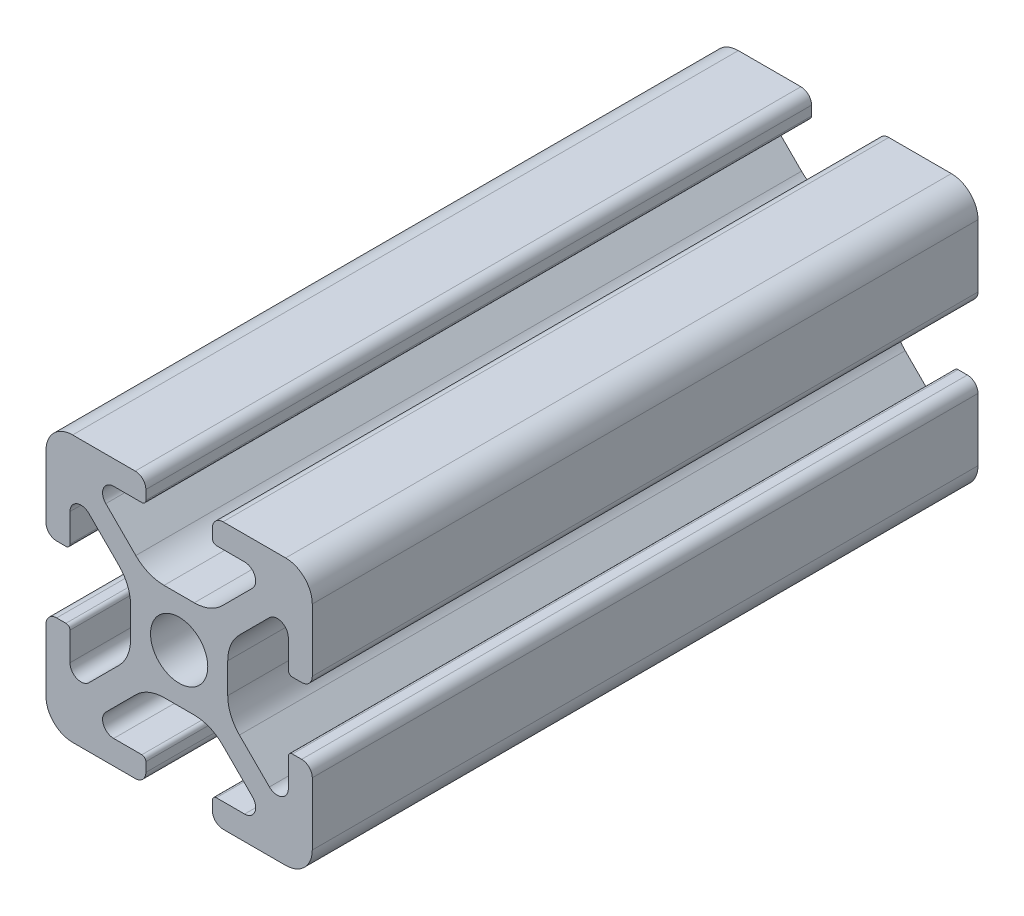
SolidWorks part; units mm, degrees
ref_plane "Front Plane" through (0, 0, 0) normal (0, 0, 1) x (1, 0, 0)
ref_plane "Top Plane" through (0, 0, 0) normal (0, 1, 0) x (1, 0, 0)
ref_plane "Right Plane" through (0, 0, 0) normal (1, 0, 0) x (0, 0, -1)
ref_plane "Plane1" through (0, 0, 0) normal (0, 0, -1) x (-1, 0, 0)
sketch "Sketch1" plane through (0, 0, 0) normal (0, 0, -1) x (-1, 0, 0)
  line L0 (-12.5, 0.8) -> (-12.5, 1.5)
  line L1 (-12.8, 1.8) -> (-14.9176, 1.8)
  line L2 (-15.5062, 3.221) -> (-13.2559, 5.4713)
  line L3 (-11.1346, 6.35) -> (-8.8654, 6.35)
  line L4 (-6.7441, 5.4713) -> (-4.4938, 3.221)
  line L5 (-5.0824, 1.8) -> (-7.2, 1.8)
  line L6 (-7.5, 1.5) -> (-7.5, 0.8)
  line L7 (-6.7, 0) -> (-2, 0)
  line L8 (0, 2) -> (0, 6.7)
  line L9 (-0.8, 7.5) -> (-1.5, 7.5)
  line L10 (-1.8, 7.2) -> (-1.8, 5.0824)
  line L11 (-3.221, 4.4938) -> (-5.4713, 6.7441)
  line L12 (-6.35, 8.8654) -> (-6.35, 11.1346)
  line L13 (-5.4713, 13.2559) -> (-3.221, 15.5062)
  line L14 (-1.8, 14.9176) -> (-1.8, 12.8)
  line L15 (-1.5, 12.5) -> (-0.8, 12.5)
  line L16 (0, 13.3) -> (0, 18)
  line L17 (-2, 20) -> (-6.7, 20)
  line L18 (-7.5, 19.2) -> (-7.5, 18.5)
  line L19 (-7.2, 18.2) -> (-5.0824, 18.2)
  line L20 (-4.4938, 16.779) -> (-6.7441, 14.5287)
  line L21 (-8.8654, 13.65) -> (-11.1346, 13.65)
  line L22 (-13.2559, 14.5287) -> (-15.5062, 16.779)
  line L23 (-14.9176, 18.2) -> (-12.8, 18.2)
  line L24 (-12.5, 18.5) -> (-12.5, 19.2)
  line L25 (-13.3, 20) -> (-18, 20)
  line L26 (-20, 18) -> (-20, 13.3)
  line L27 (-19.2, 12.5) -> (-18.5, 12.5)
  line L28 (-18.2, 12.8) -> (-18.2, 14.9176)
  line L29 (-16.779, 15.5062) -> (-14.5287, 13.2559)
  line L30 (-13.65, 11.1346) -> (-13.65, 8.8654)
  line L31 (-14.5287, 6.7441) -> (-16.779, 4.4938)
  line L32 (-18.2, 5.0824) -> (-18.2, 7.2)
  line L33 (-18.5, 7.5) -> (-19.2, 7.5)
  line L34 (-20, 6.7) -> (-20, 2)
  line L35 (-18, 0) -> (-13.3, 0)
  arc A0 (-12.5, 1.5) -> (-12.8, 1.8) centre (-12.8, 1.5) ccw
  arc A1 (-14.9176, 1.8) -> (-15.5062, 3.221) centre (-14.9176, 2.6324) cw
  arc A2 (-13.2559, 5.4713) -> (-11.1346, 6.35) centre (-11.1346, 3.35) cw
  arc A3 (-8.8654, 6.35) -> (-6.7441, 5.4713) centre (-8.8654, 3.35) cw
  arc A4 (-4.4938, 3.221) -> (-5.0824, 1.8) centre (-5.0824, 2.6324) cw
  arc A5 (-7.2, 1.8) -> (-7.5, 1.5) centre (-7.2, 1.5) ccw
  arc A6 (-7.5, 0.8) -> (-6.7, 0) centre (-6.7, 0.8) ccw
  arc A7 (-2, 0) -> (0, 2) centre (-2, 2) ccw
  arc A8 (0, 6.7) -> (-0.8, 7.5) centre (-0.8, 6.7) ccw
  arc A9 (-1.5, 7.5) -> (-1.8, 7.2) centre (-1.5, 7.2) ccw
  arc A10 (-1.8, 5.0824) -> (-3.221, 4.4938) centre (-2.6324, 5.0824) cw
  arc A11 (-5.4713, 6.7441) -> (-6.35, 8.8654) centre (-3.35, 8.8654) cw
  arc A12 (-6.35, 11.1346) -> (-5.4713, 13.2559) centre (-3.35, 11.1346) cw
  arc A13 (-3.221, 15.5062) -> (-1.8, 14.9176) centre (-2.6324, 14.9176) cw
  arc A14 (-1.8, 12.8) -> (-1.5, 12.5) centre (-1.5, 12.8) ccw
  arc A15 (-0.8, 12.5) -> (0, 13.3) centre (-0.8, 13.3) ccw
  arc A16 (0, 18) -> (-2, 20) centre (-2, 18) ccw
  arc A17 (-6.7, 20) -> (-7.5, 19.2) centre (-6.7, 19.2) ccw
  arc A18 (-7.5, 18.5) -> (-7.2, 18.2) centre (-7.2, 18.5) ccw
  arc A19 (-5.0824, 18.2) -> (-4.4938, 16.779) centre (-5.0824, 17.3676) cw
  arc A20 (-6.7441, 14.5287) -> (-8.8654, 13.65) centre (-8.8654, 16.65) cw
  arc A21 (-11.1346, 13.65) -> (-13.2559, 14.5287) centre (-11.1346, 16.65) cw
  arc A22 (-15.5062, 16.779) -> (-14.9176, 18.2) centre (-14.9176, 17.3676) cw
  arc A23 (-12.8, 18.2) -> (-12.5, 18.5) centre (-12.8, 18.5) ccw
  arc A24 (-12.5, 19.2) -> (-13.3, 20) centre (-13.3, 19.2) ccw
  arc A25 (-18, 20) -> (-20, 18) centre (-18, 18) ccw
  arc A26 (-20, 13.3) -> (-19.2, 12.5) centre (-19.2, 13.3) ccw
  arc A27 (-18.5, 12.5) -> (-18.2, 12.8) centre (-18.5, 12.8) ccw
  arc A28 (-18.2, 14.9176) -> (-16.779, 15.5062) centre (-17.3676, 14.9176) cw
  arc A29 (-14.5287, 13.2559) -> (-13.65, 11.1346) centre (-16.65, 11.1346) cw
  arc A30 (-13.65, 8.8654) -> (-14.5287, 6.7441) centre (-16.65, 8.8654) cw
  arc A31 (-16.779, 4.4938) -> (-18.2, 5.0824) centre (-17.3676, 5.0824) cw
  arc A32 (-18.2, 7.2) -> (-18.5, 7.5) centre (-18.5, 7.2) ccw
  arc A33 (-19.2, 7.5) -> (-20, 6.7) centre (-19.2, 6.7) ccw
  arc A34 (-20, 2) -> (-18, 0) centre (-18, 2) ccw
  arc A35 (-13.3, 0) -> (-12.5, 0.8) centre (-13.3, 0.8) ccw
  circle A36 centre (-10, 10) radius 2.15
extrude "Boss-Extrude1" add sketch "Sketch1" against normal blind 50
equation "\"plate_thickness\" = 6.35 'thickness of the plate "
equation "\"t_height\" = 200"
equation "\"t_width\" = 240"
equation "\"t_length\" = 240"
equation "\"D1@Boss-Extrude1\"=\"perce_t_height\""
equation "\"connector_D1\" = 70 'the big holes diameter"
equation "\"mtg_hole_D\" = 5.5 'mounting holes"
equation "\"mtg_dfc\" = 40 'mounting hole distance from center"
equation "\"plate_hole_from_edge\" = 9"
equation "\"plate_spacing\" = 1"
equation "\"front_plate_height\" = \"t_height\" + 38"
equation "\"front_plate_width\" = \"t_width\" + 38"
equation "\"side_plate_height\" = \"front_plate_height\""
equation "\"side_plate_length\" = \"t_length\" + 38"
equation "\"top_plate_width\" = \"front_plate_width\""
equation "\"top_plate_length\" = \"side_plate_length\""
equation "\"itx_support_t_slot_length\" = \"t_width\" + (2 * 20.5)"
equation "\"locomotion_length\" = \"t_length\""
equation "\"locomotion_width\" = \"t_width\""
equation "\"locomotion_height\" = 40"
equation "\"itx_mtg_hole_spacing\" = 40"
equation "\"emg30_bracket_hole_len\" = 60"
equation "\"emg30_bracket_hole_wid\" = 11"
equation "\"perce_t_height\" = 50"
equation "\"perce_top_width\" = 150"
equation "\"perce_mtg_hole_spacing\" = \"perce_top_width\" - 20"
